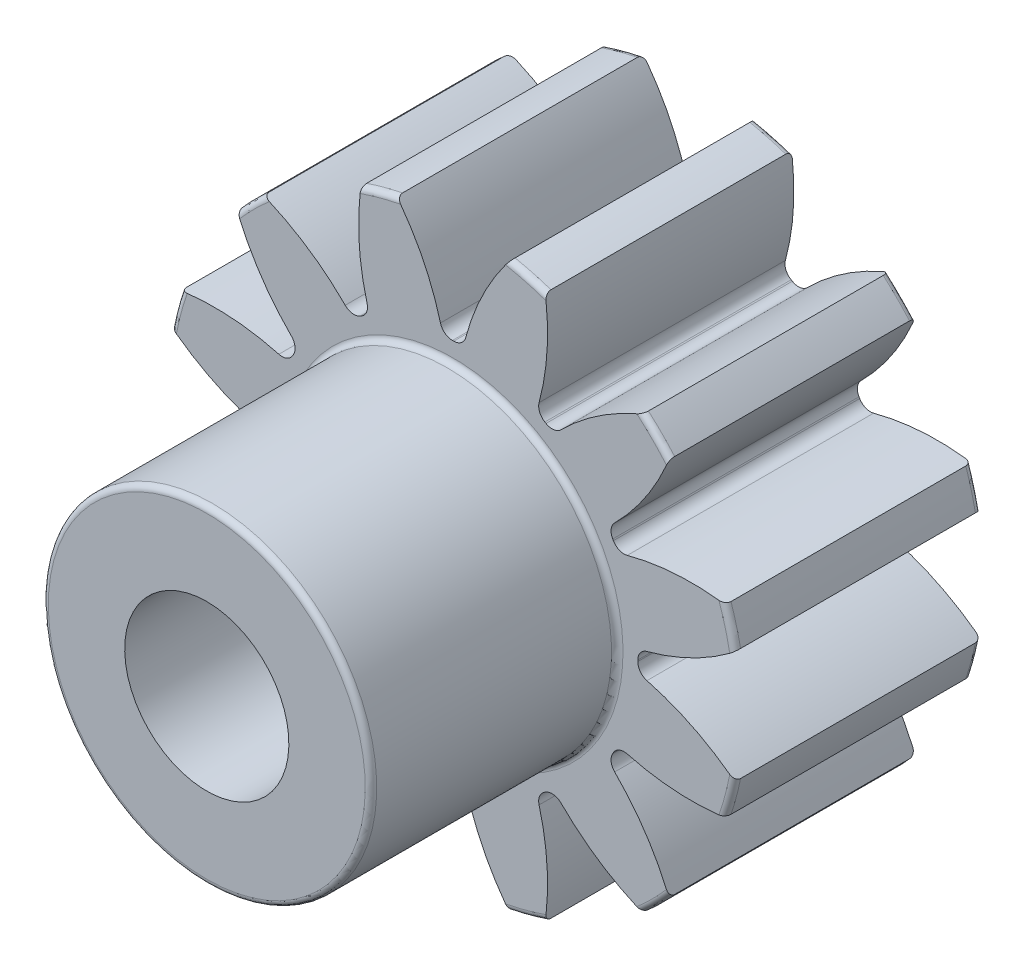
SolidWorks part; units mm, degrees
ref_plane "Front Plane" through (0, 0, 0) normal (0, 0, 1) x (1, 0, 0)
ref_plane "Top Plane" through (0, 0, 0) normal (0, 1, 0) x (1, 0, 0)
ref_plane "Right Plane" through (0, 0, 0) normal (1, 0, 0) x (0, 0, -1)
sketch "Sketch1" plane through (0, 0, 0) normal (0, 0, 1) x (1, 0, 0)
  line L0 (-152.4, 0) -> (152.4, 0) construction
  circle A0 centre (0, 0) radius 7 construction
  circle A1 centre (0, 0) radius 6 construction
  circle A2 centre (0, 0) radius 4.5 construction
  circle A3 centre (0, 0) radius 4 construction
  circle A4 centre (0, 0) radius 2 construction
  dimension "D2" = 1
  dimension "D3" = 2.5
  dimension "D1" = 2.5
sketch "Sketch2" plane through (0, 0, 0) normal (1, 0, 0) x (0, 0, -1)
  line L0 (0, 0) -> (-6, 0) construction
  line L1 (-6, 0) -> (-12, 0) construction
  dimension "Overall Width" = 12
  dimension "Face Width" = 6
sketch "Sketch4" plane through (0, 0, 0) normal (1, 0, 0) x (0, 0, -1)
  line L0 (-12, 2) -> (-12, 4)
  line L1 (-12, 4) -> (-6, 4)
  line L2 (-6, 4) -> (-6, 7)
  line L3 (-6, 7) -> (0, 7)
  line L4 (0, 7) -> (0, 2)
  line L5 (-6, 4) -> (-6, 0) construction
  line L6 (0, 7) -> (0, -7) construction
  line L7 (-6, 4) -> (0, 4) construction
  line L12 (-12, 2) -> (0, 2)
revolve "Revolve1" add sketch "Sketch4" angle 360 about L1
fillet "Fillet2" radius 0.14 4 edges at (0, 4, 12) (0, 4, 6) (0, 7, 6) (0, 7, 0)
sketch "Sketch7" plane through (0, 0, 6) normal (0, 0, 1) x (1, 0, 0)
  line L0 (0, 0) -> (0, 7) construction
  line L1 (0.7832, 5.9487) -> (1.27, 6.8838) construction
  line L3 (1.8117, 6.7615) -> (1.5529, 5.7956) construction
  line L4 (1.5529, 5.7956) -> (1.1647, 4.3467) construction
  line L5 (0, 0) -> (1.1647, 4.3467) construction
  line L6 (0.7832, 5.9487) -> (0, 0) construction
  line L7 (0.7832, 5.9487) -> (0.9137, 6.9401) construction
  line L8 (0.7832, 5.9487) -> (0, 0) construction
  circle A0 centre (0, 0) radius 7 construction
  arc A1 (-0.0164, 4.5) -> (0.0164, 4.5) centre (0, 0) cw
  circle A2 centre (0, 0) radius 4.5 construction
  arc A3 (-0.7832, 5.9487) -> (0.7832, 5.9487) centre (0, 0) cw construction
  circle A4 centre (0, 0) radius 6 construction
  arc A5 (2.2448, 6.6303) -> (1.3711, 6.8644) centre (0, 0) ccw construction
  arc A6 (0.7832, 5.9487) -> (2.2961, 5.5433) centre (0, 0) cw construction
  arc A7 (-1.3711, 6.8644) -> (1.3711, 6.8644) centre (0, 0) cw
  arc A8 (0.3074, 4.7228) -> (1.3711, 6.8644) centre (6.1052, 3.1782) cw
  arc A9 (-0.3074, 4.7228) -> (-1.3711, 6.8644) centre (-6.1052, 3.1782) ccw
  arc A10 (-0.0164, 4.5) -> (-0.3074, 4.7228) centre (-0.0175, 4.8) cw
  arc A11 (0.0164, 4.5) -> (0.3074, 4.7228) centre (0.0175, 4.8) ccw
  point P26 (-0.2511, 4.493)
  point P29 (0.2511, 4.493)
  dimension "D4" = 0.3
  dimension "D5" = 6
  dimension "D3" = 20
  dimension "D1" = 3.1416
  dimension "D2" = 1.5708
extrude "Cut-Extrude2" cut sketch "Sketch7" against normal through all
pattern_circular "CirPattern1" count 12 over 360 about axis through (0, 0, 0) along (0, 0, 1) of "Cut-Extrude2"
equation "\"D1@Sketch1\"=2.5*(\"Pitch Dia.@Sketch1\"/\"Number of Teeth@Sketch1\")"
equation "\"D1@CirPattern1\"=\"Number of Teeth@Sketch1\""
equation "\"D1@Fillet2\"=\"OD@Sketch1\"*.01"
equation "\"D1@Sketch7\"=3.14159*(\"Pitch Dia.@Sketch1\"/\"Number of Teeth@Sketch1\")"
equation "\"D2@Sketch7\"=\"D1@Sketch7\"/2"
equation "\"D4@Sketch7\"=\"D1@Sketch7\"*.0955"
equation "\"D5@Sketch7\"=\"Pitch Dia.@Sketch1\"/2"
